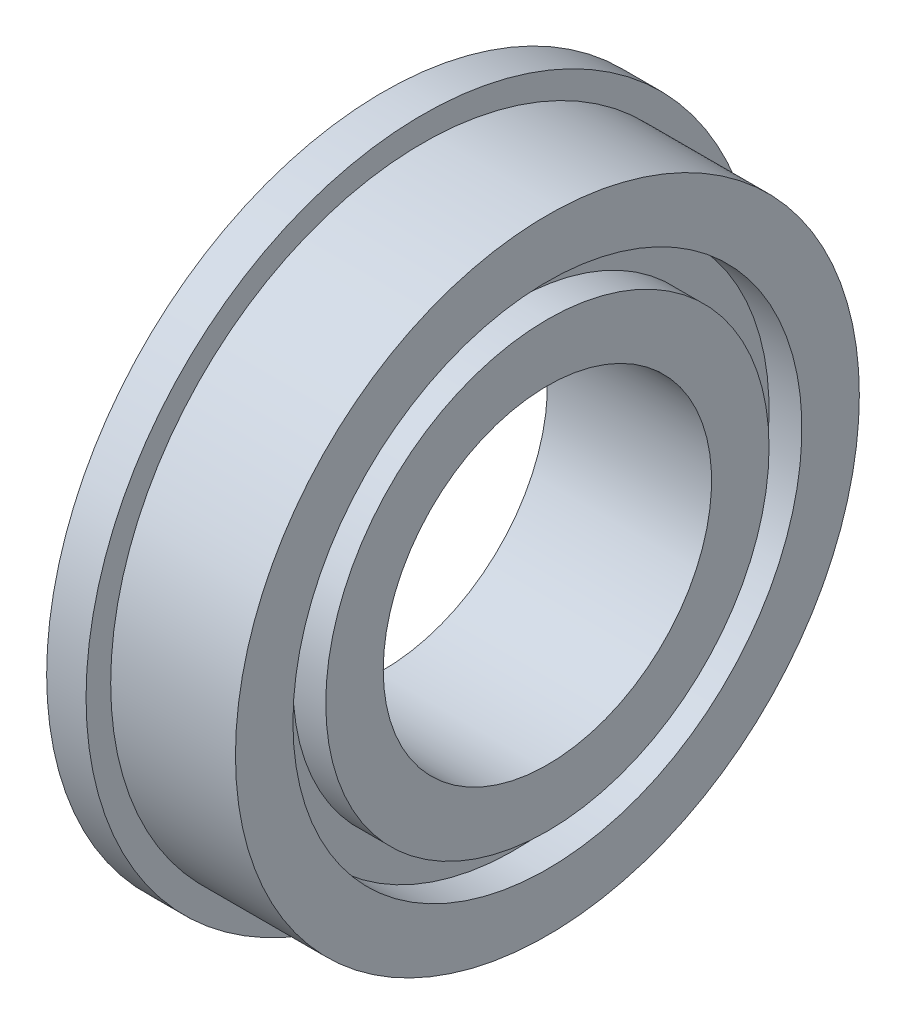
SolidWorks part; units mm, degrees
material "AISI 304"
ref_plane "Front Plane" through (0, 0, 0) normal (0, 0, 1) x (1, 0, 0)
ref_plane "Top Plane" through (0, 0, 0) normal (0, 1, 0) x (1, 0, 0)
ref_plane "Right Plane" through (0, 0, 0) normal (1, 0, 0) x (0, 0, -1)
sketch "Sketch2" plane through (0, 0, 0) normal (0, 0, 1) x (1, 0, 0)
  line L0 (0, 0) -> (12.0838, 0) construction
  line L1 (-1.2, 10.25) -> (0, 10.25)
  line L2 (-1.2, 10.25) -> (-1.2, 7.75)
  line L3 (-1.2, 5) -> (3.8, 5)
  line L4 (3.8, 9.5) -> (3.8, 7.75)
  line L5 (-1.2, 6.75) -> (-1.2, 5)
  line L6 (0, 10.25) -> (0, 9.5)
  line L7 (0, 9.5) -> (3.8, 9.5)
  line L8 (3.8, 6.75) -> (3.8, 5)
  line L9 (-1.2, 6.75) -> (-0.2, 6.75)
  line L10 (0, 9.5) -> (0, 0) construction
  line L11 (-1.2, 7.75) -> (-0.2, 7.75)
  line L12 (-0.2, 6.75) -> (-0.2, 7.75)
  line L13 (3.8, 7.75) -> (2.8, 7.75)
  line L15 (3.8, 6.75) -> (2.8, 6.75)
  line L16 (2.8, 7.75) -> (2.8, 6.75)
  dimension "D1" = 10
  dimension "D2" = 19
  dimension "D3" = 1
  dimension "D4" = 5
  dimension "D5" = 1.2
  dimension "D6" = 20.5
  dimension "D7" = 1
revolve "Revolve1" add sketch "Sketch2" angle 360 about L0
